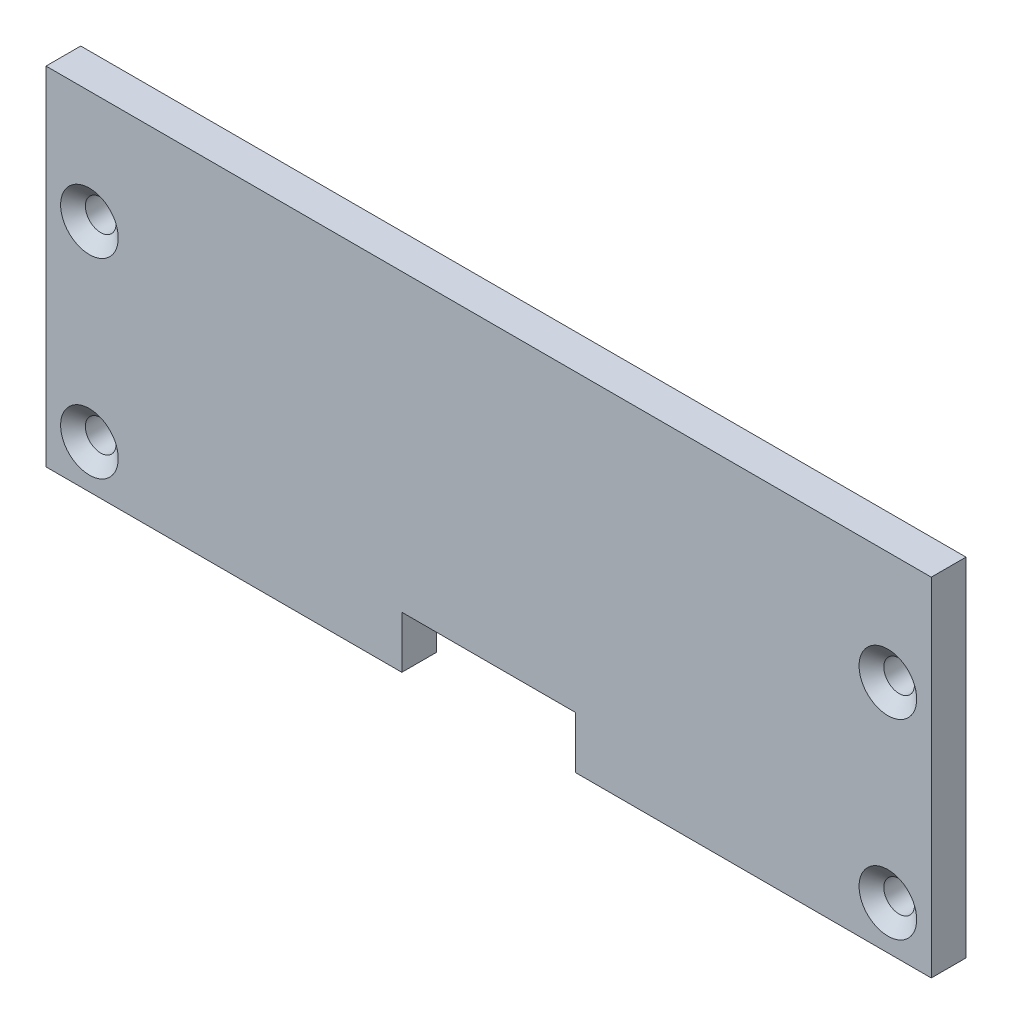
SolidWorks part; units mm, degrees
ref_plane "Front Plane" through (0, 0, 0) normal (0, 0, 1) x (1, 0, 0)
ref_plane "Top Plane" through (0, 0, 0) normal (0, 1, 0) x (1, 0, 0)
ref_plane "Right Plane" through (0, 0, 0) normal (1, 0, 0) x (0, 0, -1)
sketch "Sketch1" plane through (0, 0, 0) normal (0, 0, 1) x (1, 0, 0)
  line L1 (-64.77, -25.4) -> (64.77, -25.4)
  line L2 (-64.77, -25.4) -> (-64.77, 25.4)
  line L3 (-64.77, 25.4) -> (64.77, 25.4)
  line L4 (64.77, -25.4) -> (64.77, 25.4)
  line L5 (0, 25.4) -> (0, -25.4) construction
  line L6 (-64.77, 0) -> (64.77, 0) construction
  point P0 (0, 0)
  dimension "D1" = 129.54
  dimension "D2" = 50.8
extrude "Boss-Extrude1" add sketch "Sketch1" along normal blind 5.08
hole_wizard "CSK for #8 Flat Head Machine Screw (100)1" positions "Sketch4" profile "Sketch3" countersink size "#8" standard "ANSI Inch" end condition through all
sketch "Sketch4" plane through (0, 0, 5.08) normal (0, 0, 1) x (1, 0, 0)
  line L0 (64.77, 25.4) -> (-64.77, 25.4) construction
  line L1 (-64.77, 25.4) -> (-64.77, -25.4) construction
  line L2 (-64.77, -25.4) -> (64.77, -25.4) construction
  line L3 (64.77, -25.4) -> (64.77, 25.4) construction
  point P0 (-58.42, 8.89)
  point P2 (-58.42, -19.05)
  point P4 (58.42, -19.05)
  point P6 (58.42, 8.89)
  dimension "D1" = 16.51
  dimension "D2" = 6.35
  dimension "D3" = 6.35
  dimension "D4" = 6.35
sketch "Sketch3" plane through (-58.42, 8.89, 5.08) normal (1, 0, 0) x (0, -1, 0)
  line L0 (0, 0) -> (0, 5.08)
  line L1 (0, 5.08) -> (2.2479, 5.08)
  line L2 (2.2479, 5.08) -> (2.2479, 1.6518)
  line L3 (2.2479, 1.6518) -> (4.2164, 0)
  line L5 (4.2164, 0) -> (0, 0)
  line L6 (-2.2479, 1.6518) -> (-4.2164, 0) construction
  line L11 (0, -6.35) -> (0, 107.95) construction
  dimension "Thru Hole Dia." = 4.4958
  dimension "Thru Hole Depth" = 5.08
  dimension "Near C'Sink Dia." = 8.4328
  dimension "Near C'Sink Angle" = 100
sketch "Sketch5" plane through (0, 0, 5.08) normal (0, 0, 1) x (1, 0, 0)
  line L0 (-64.77, -25.4) -> (64.77, -25.4) construction
  line L1 (-12.7, -25.4) -> (12.7, -25.4)
  line L2 (-12.7, -25.4) -> (-12.7, -17.78)
  line L3 (-12.7, -17.78) -> (12.7, -17.78)
  line L4 (12.7, -25.4) -> (12.7, -17.78)
  line L5 (0, -17.78) -> (0, -25.4) construction
  line L6 (-12.7, -21.59) -> (12.7, -21.59) construction
  point P0 (0, -21.59)
  dimension "D1" = 7.62
  dimension "D2" = 25.4
  dimension "D3" = 0
extrude "Cut-Extrude1" cut sketch "Sketch5" against normal through all
